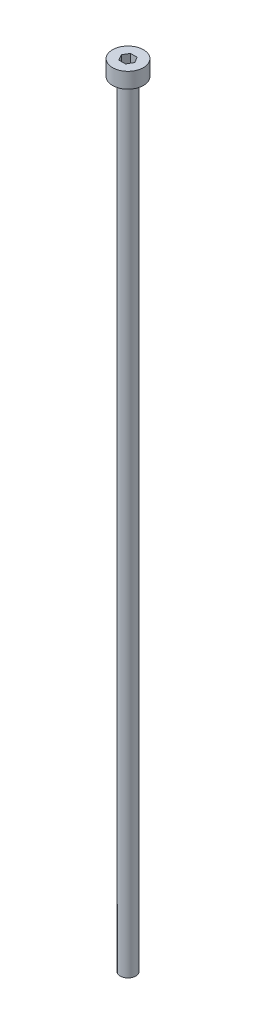
SolidWorks part; units mm, degrees
material "AISI 304"
ref_plane "前视基准面" through (0, 0, 0) normal (0, 0, 1) x (1, 0, 0)
ref_plane "上视基准面" through (0, 0, 0) normal (0, 1, 0) x (1, 0, 0)
ref_plane "右视基准面" through (0, 0, 0) normal (1, 0, 0) x (0, 0, -1)
sketch "草图1" plane through (0, 0, 0) normal (0, 1, 0) x (1, 0, 0)
  circle A0 centre (0, 0) radius 2
  dimension "D1" = 4
extrude "杯头高度" add sketch "草图1" along normal blind 2
sketch "草图2" plane through (0, 2, 0) normal (0, 1, 0) x (1, 0, 0)
  line L1 (0.866, 0) -> (0.433, 0.75)
  line L2 (0.433, 0.75) -> (-0.433, 0.75)
  line L3 (-0.433, 0.75) -> (-0.866, 0)
  line L4 (-0.866, 0) -> (-0.433, -0.75)
  line L5 (-0.433, -0.75) -> (0.433, -0.75)
  line L6 (0.433, -0.75) -> (0.866, 0)
  circle A0 centre (0, 0) radius 0.75 construction
  dimension "D1" = 1.5
extrude "内六角深度" cut sketch "草图2" against normal blind 1.5
sketch "草图3" plane through (0, 0, 0) normal (0, -1, 0) x (1, 0, 0)
  circle A0 centre (0, 0) radius 1
  dimension "D1" = 2
extrude "螺纹长度" add sketch "草图3" along normal blind 100
